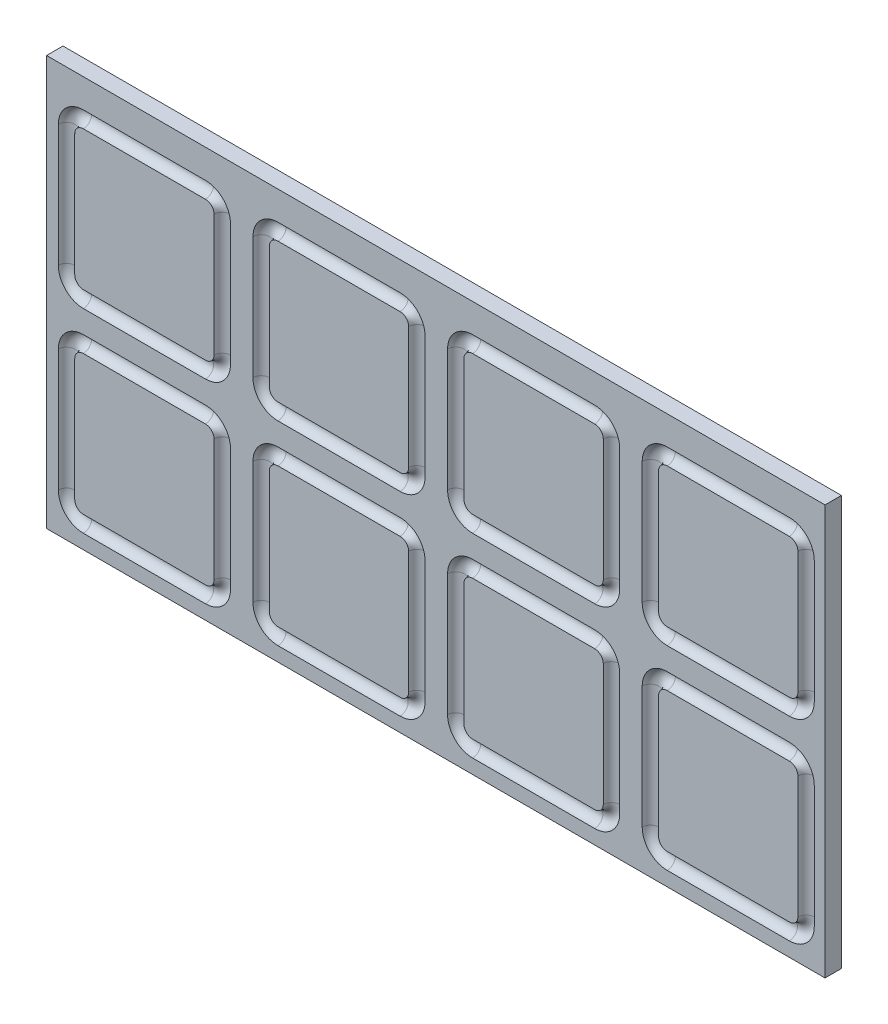
SolidWorks part; units mm, degrees
ref_plane "Front" through (0, 0, 0) normal (0, 0, 1) x (1, 0, 0)
ref_plane "Top" through (0, 0, 0) normal (0, 1, 0) x (1, 0, 0)
ref_plane "Right" through (0, 0, 0) normal (1, 0, 0) x (0, 0, -1)
sketch "Sketch1" plane through (0, 0, 0) normal (0, 0, 1) x (1, 0, 0)
  line L1 (29.8, 38) -> (-29.8, 38)
  line L2 (38, 29.8) -> (38, -29.8)
  line L3 (29.8, -38) -> (-29.8, -38)
  line L4 (-38, 29.8) -> (-38, -29.8)
  line L5 (38, 38) -> (-38, -38) construction
  line L7 (38, -38) -> (-38, 38) construction
  arc A0 (29.8, 38) -> (38, 29.8) centre (29.8, 29.8) cw
  arc A1 (38, -29.8) -> (29.8, -38) centre (29.8, -29.8) cw
  arc A2 (-29.8, -38) -> (-38, -29.8) centre (-29.8, -29.8) cw
  arc A3 (-29.8, 38) -> (-38, 29.8) centre (-29.8, 29.8) ccw
  point P0 (0, 0)
  dimension "D3" = 8.2
  dimension "D1" = 76
  dimension "D2" = 76
sketch "Sketch3" plane through (0, 0, 0) normal (0, 0, 1) x (1, 0, 0)
  line L1 (332.2481, -143.9766) -> (-47.7519, -143.9766)
  line L2 (332.2481, -143.9766) -> (332.2481, 56.0234)
  line L3 (332.2481, 56.0234) -> (-47.7519, 56.0234)
  line L4 (-47.7519, -143.9766) -> (-47.7519, 56.0234)
  line L5 (332.2481, -143.9766) -> (-47.7519, 56.0234) construction
  line L6 (332.2481, 56.0234) -> (-47.7519, -143.9766) construction
  point P0 (0, 0)
  dimension "D1" = 200
  dimension "D2" = 380
extrude "Boss-Extrude1" add sketch "Sketch3" against normal blind 8
sketch "Sketch6" plane through (0, 0, 0) normal (0, 1, 0) x (1, 0, 0)
  line L0 (38, 0) -> (-38, 0) construction
  line L1 (332.2481, 0) -> (-47.7519, 0) construction
  circle A0 centre (-38, 0) radius 4
sweep "Cut-Sweep11" cut profiles "Sketch6" path "Sketch1"
pattern_linear "LPattern1" count 4 spacing 95 along (1, 0, 0) count 2 spacing 95 along (0, -1, 0) of "Cut-Sweep11"
